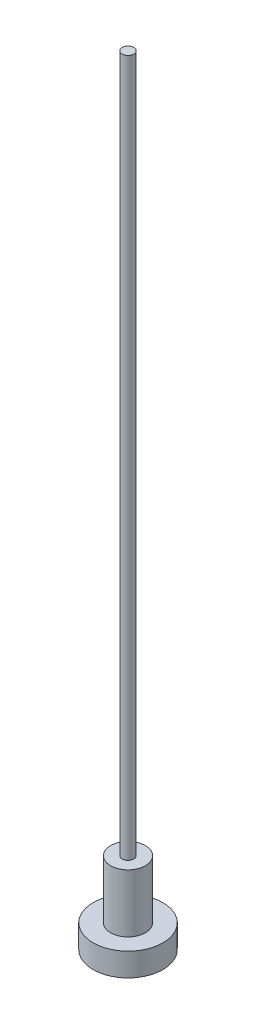
SolidWorks part; units mm, degrees
ref_plane "Front Plane" through (0, 0, 0) normal (0, 0, 1) x (1, 0, 0)
ref_plane "Top Plane" through (0, 0, 0) normal (0, 1, 0) x (1, 0, 0)
ref_plane "Right Plane" through (0, 0, 0) normal (1, 0, 0) x (0, 0, -1)
sketch "Sketch2" plane through (0, 0, 0) normal (0, 1, 0) x (1, 0, 0)
  circle A0 centre (0, 0) radius 1.5
  dimension "D1" = 3
extrude "Boss-Extrude1" add sketch "Sketch2" along normal blind 5
sketch "Sketch3" plane through (0, 5, 0) normal (0, 1, 0) x (1, 0, 0)
  circle A0 centre (0, 0) radius 0.5
  dimension "D1" = 1
extrude "Boss-Extrude2" add sketch "Sketch3" along normal blind 60
sketch "Sketch4" plane through (0, 0, 0) normal (0, -1, 0) x (1, 0, 0)
  circle A0 centre (0, 0) radius 3
  dimension "D1" = 6
extrude "Boss-Extrude3" add sketch "Sketch4" along normal blind 2
